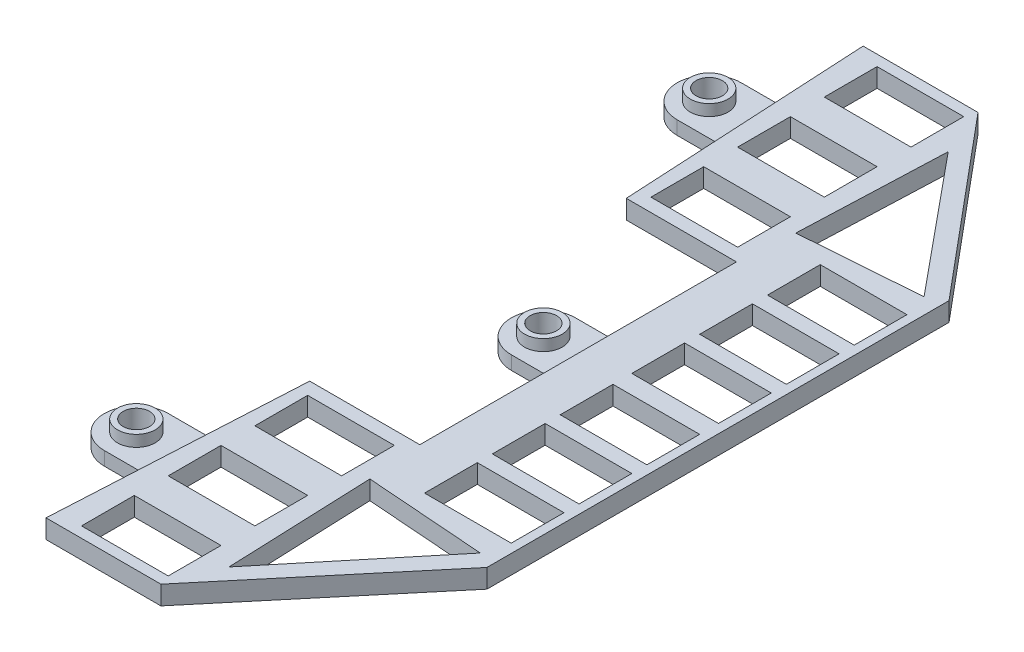
SolidWorks part; units mm, degrees
ref_plane "Plano frontal" through (0, 0, 0) normal (0, 0, 1) x (1, 0, 0)
ref_plane "Plano superior" through (0, 0, 0) normal (0, 1, 0) x (1, 0, 0)
ref_plane "Plano direito" through (0, 0, 0) normal (1, 0, 0) x (0, 0, -1)
sketch "Esboço1" plane through (0, 0, 0) normal (0, 1, 0) x (1, 0, 0)
  line L0 (6, 17.9) -> (8, 17.9) construction
  line L1 (-8, -33) -> (8, -33) construction
  line L2 (-8, -33) -> (-8, 33) construction
  line L3 (-8, 33) -> (8, 33) construction
  line L4 (8, -33) -> (8, 33) construction
  line L5 (-8, -33) -> (8, 33) construction
  line L6 (-8, 33) -> (8, -33) construction
  line L7 (4.5, 19.4) -> (4.5, 33) construction
  line L8 (4.5, -19.6) -> (4.5, -33) construction
  line L9 (4.5, -16.6) -> (8, -16.6)
  line L10 (4.5, -19.6) -> (8, -19.6)
  line L11 (4.5, 16.4) -> (8, 16.4)
  line L12 (4.5, 19.4) -> (8, 19.4)
  line L13 (8, -16.6) -> (8, -14.8)
  line L14 (8, 16.4) -> (8, 15.3)
  line L15 (-8, 33) -> (-8, -33)
  line L16 (-8, -33) -> (8, -33)
  line L17 (8, -33) -> (8, -19.6)
  line L18 (-8, 33) -> (8, 33)
  line L19 (8, 33) -> (8, 19.4)
  line L20 (8, 15.3) -> (1, 15.3)
  line L21 (1, 15.3) -> (1, -14.8)
  line L22 (1, -14.8) -> (8, -14.8)
  line L23 (-8, -33) -> (-24.3938, -54.2)
  line L24 (-24.3938, -54.2) -> (-9.15, -54.2)
  line L26 (-8, 33) -> (-24.3938, 54.2)
  line L27 (-24.3938, 54.2) -> (-9.15, 54.2)
  line L28 (-9.15, 54.2) -> (10.5532, 30.65)
  line L29 (10.5532, 30.65) -> (10.5532, -30.65)
  line L30 (10.5532, -30.65) -> (-9.15, -54.2)
  line L32 (-8, -21) -> (-22.6103, -21)
  line L33 (-22.6103, -21) -> (-24.3938, -54.2)
  line L34 (-8, 21) -> (-22.6103, 21)
  line L35 (-22.6103, 21) -> (-24.3938, 54.2)
  line L36 (0, -55) -> (0, 55) construction
  circle A0 centre (4.5, 17.9) radius 1.5 construction
  circle A1 centre (4.5, -18.1) radius 1.5 construction
  arc A2 (4.5, 19.4) -> (4.5, 16.4) centre (4.5, 17.9) ccw
  arc A3 (4.5, -19.6) -> (4.5, -16.6) centre (4.5, -18.1) cw
  point P0 (0, 0)
  dimension "D3" = 3
  dimension "D4" = 2
  dimension "D1" = 66
  dimension "D2" = 16
  dimension "D5" = 13.6
  dimension "D6" = 13.4
  dimension "D7" = 7
  dimension "D8" = 1.8
  dimension "D9" = 1.1
  dimension "D10" = 12
  dimension "D11" = 54.2
  dimension "D12" = 12
  dimension "D13" = 54.2
  dimension "D14" = 30.65
  dimension "D15" = 30.65
  dimension "D16" = 9.15
extrude "Ressalto-extrusão1" add sketch "Esboço1" along normal mid plane 2.5
sketch "Esboço5" plane through (0, 1.25, 0) normal (0, 1, 0) x (1, 0, 0)
  line L0 (-55, 0) -> (55, 0) construction
  line L1 (-1.3757, -7.5) -> (8.6243, -7.5) construction
  line L2 (-1.3757, -7.5) -> (-1.3757, -2) construction
  line L3 (-1.3757, -2) -> (8.6243, -2) construction
  line L4 (8.6243, -7.5) -> (8.6243, -2) construction
  line L5 (-2.1257, -8.25) -> (9.3743, -8.25)
  line L6 (-2.1257, -8.25) -> (-2.1257, -1.25)
  line L7 (-2.1257, -1.25) -> (9.3743, -1.25)
  line L8 (9.3743, -8.25) -> (9.3743, -1.25)
  point P8 (9.3743, -4.75)
  point P9 (8.6243, -4.75)
  point P10 (3.6243, -7.5)
  point P11 (3.6243, -8.25)
  dimension "D1" = 10
  dimension "D2" = 5.5
  dimension "D3" = 0.75
  dimension "D4" = 0.75
  dimension "D5" = 8.25
  dimension "D6" = 7.5
extrude "Corte-extrusão1" cut sketch "Esboço5" against normal up to next (2.5 mm away)
pattern_linear "Padrão linear1" count 3 spacing 9 along (0, 0, 1) of "Corte-extrusão1"
sketch "Esboço8" plane through (0, 1.25, 0) normal (0, 1, 0) x (1, 0, 0)
  line L0 (-55, 0) -> (55, 0) construction
  line L1 (-21.11, 22.77) -> (-9.61, 22.77)
  line L2 (-21.11, 22.77) -> (-21.11, 29.77)
  line L3 (-21.11, 29.77) -> (-9.61, 29.77)
  line L4 (-9.61, 22.77) -> (-9.61, 29.77)
  line L5 (0, -55) -> (0, 55) construction
  dimension "D1" = 11.5
  dimension "D2" = 7
  dimension "D3" = 22.77
  dimension "D4" = 21.11
extrude "Corte-extrusão4" cut sketch "Esboço8" against normal blind 10
pattern_linear "Padrão linear3" count 3 spacing 11.5 along (0, 0, -1) of "Corte-extrusão4"
mirror "Espelhar1" about plane through (0, 0, 0) normal (0, 0, 1) of "Padrão linear3", "Corte-extrusão4"
mirror "Espelhar2" about plane through (0, 0, 0) normal (0, 0, 1) of "Padrão linear1", "Corte-extrusão1"
sketch "Esboço9" plane through (0, 1.25, 0) normal (0, 1, 0) x (1, 0, 0)
  line L0 (8.4557, -29.4356) -> (-7.3759, -28.2521)
  line L1 (-7.3759, -28.2521) -> (-6.6092, -47.7109)
  line L2 (-6.6092, -47.7109) -> (8.4557, -29.4356)
extrude "Corte-extrusão5" cut sketch "Esboço9" against normal blind 10
mirror "Espelhar3" about plane through (0, 0, 0) normal (0, 0, 1) of "Corte-extrusão5"
sketch "Esboço10" plane through (0, 0, 0) normal (0, 1, 0) x (1, 0, 0)
  line L0 (-28.61, -33.75) -> (-23.2952, -33.75)
  line L1 (-22.6103, -21) -> (-24.3938, -54.2) construction
  line L2 (-28.61, -42.25) -> (-23.7518, -42.25)
  line L3 (-23.7518, -42.25) -> (-23.2952, -33.75)
  line L4 (-21.11, -41.27) -> (-21.11, -34.27) construction
  line L5 (-28.61, -33.75) -> (-28.61, -36.25) construction
  circle A0 centre (-28.61, -38) radius 1.75
  arc A1 (-28.61, -33.75) -> (-28.61, -42.25) centre (-28.61, -38) ccw
  dimension "D1" = 3.5
  dimension "D2" = 7.5
  dimension "D3" = 2.5
  dimension "D4" = 38
extrude "Ressalto-extrusão2" add sketch "Esboço10" along normal mid plane 1.8
sketch "Esboço11" plane through (0, 0.9, 0) normal (0, 1, 0) x (1, 0, 0)
  circle A2 centre (-28.61, -38) radius 1.75
  circle A3 centre (-28.61, -38) radius 1.75 construction
  circle A4 centre (-28.61, -38) radius 2.5
  dimension "D1" = 5
extrude "Ressalto-extrusão3" add sketch "Esboço11" along normal blind 1.5
mirror "Espelhar4" about plane through (0, 0, 0) normal (0, 1, 0) of "Ressalto-extrusão3"
pattern_linear "Padrão linear4" count 2 spacing 38 along (0, 0, 1) count 2 spacing 16 along (1, 0, 0) of "Ressalto-extrusão2", "Ressalto-extrusão3", "Espelhar4"
mirror "Espelhar5" about plane through (0, 0, 0) normal (0, 0, 1) of "Espelhar4", "Ressalto-extrusão3", "Ressalto-extrusão2"
